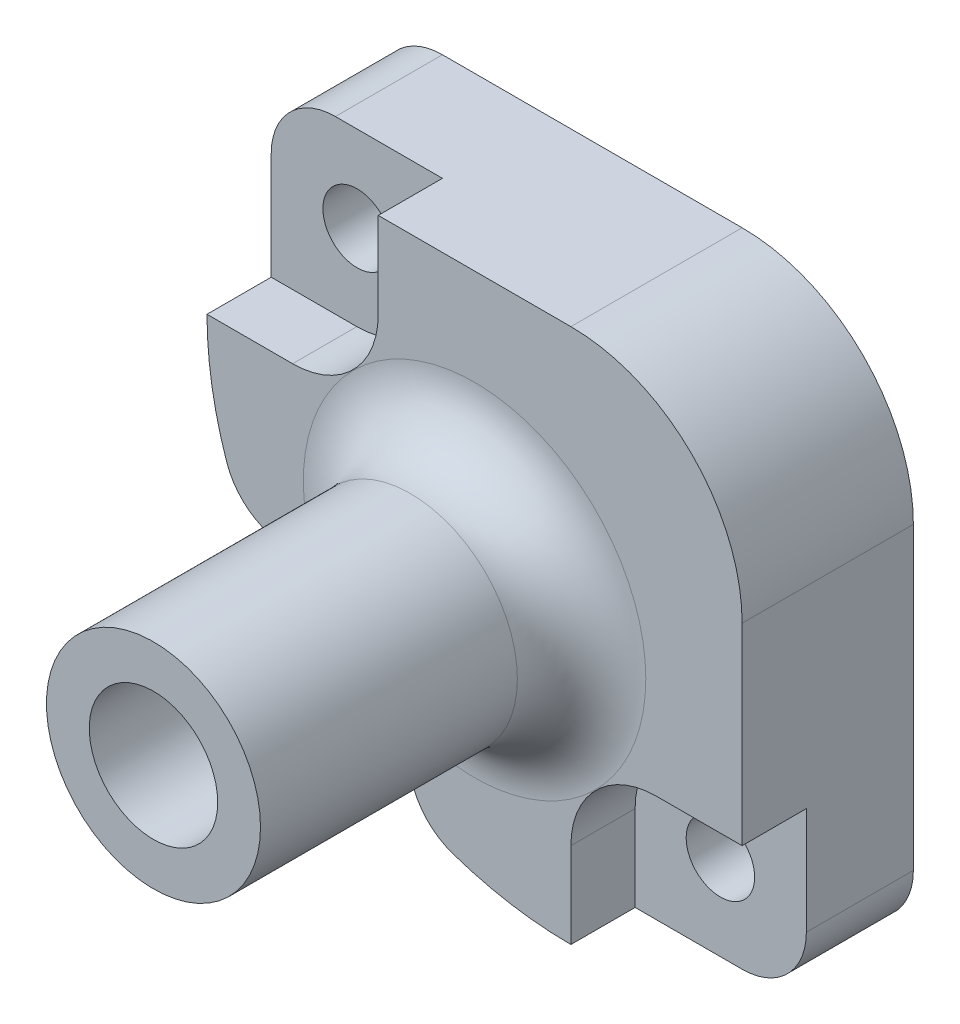
SolidWorks part; units mm, degrees
ref_plane "Piano frontale" through (0, 0, 0) normal (0, 0, 1) x (1, 0, 0)
ref_plane "Piano superiore" through (0, 0, 0) normal (0, 1, 0) x (1, 0, 0)
ref_plane "Piano destro" through (0, 0, 0) normal (1, 0, 0) x (0, 0, -1)
sketch "Schizzo1" plane through (0, 0, 0) normal (0, 0, 1) x (1, 0, 0)
  line L1 (-12.5, 12.5) -> (12.5, 12.5)
  line L2 (-12.5, 12.5) -> (-12.5, -12.5)
  line L3 (-12.5, -12.5) -> (12.5, -12.5)
  line L4 (12.5, 12.5) -> (12.5, -12.5)
  line L5 (-12.5, 12.5) -> (12.5, -12.5) construction
  line L6 (-12.5, -12.5) -> (12.5, 12.5) construction
  point P0 (0, 0)
  dimension "D1" = 25
extrude "Estrusione-Estrusione1" add sketch "Schizzo1" along normal blind 8
sketch "Schizzo8" plane through (0, 0, 8) normal (0, 0, 1) x (1, 0, 0)
  circle A0 centre (0, 0) radius 5
  dimension "D1" = 10
extrude "Estrusione-Estrusione3" add sketch "Schizzo8" along normal blind 15
fillet "Raccordo1" radius 3 1 edges at (5, 0, 8)
sketch "Schizzo9" plane through (0, 0, 0) normal (0, 0, -1) x (-1, 0, 0)
  circle A0 centre (0, 0) radius 1.6
  dimension "D1" = 3.2
extrude "Taglio-Estrusione2" cut sketch "Schizzo9" against normal up to next
sketch "Schizzo10" plane through (0, 0, 0) normal (0, 0, -1) x (-1, 0, 0)
  circle A0 centre (0, 0) radius 3
  dimension "D1" = 6
extrude "Taglio-Estrusione3" cut sketch "Schizzo10" against normal blind 4
sketch "Schizzo11" plane through (0, 0, 23) normal (0, 0, 1) x (1, 0, 0)
  circle A0 centre (0, 0) radius 3
  dimension "D1" = 6
extrude "Taglio-Estrusione4" cut sketch "Schizzo11" against normal blind 16
sketch "Schizzo13" plane through (0, 0, 0) normal (0, 0, -1) x (-1, 0, 0)
  line L0 (-12.5, -12.5) -> (12.5, 12.5) construction
  circle A0 centre (0, 0) radius 12 construction
  circle A1 centre (-8.4853, -8.4853) radius 1.6
  circle A2 centre (8.4853, 8.4853) radius 1.6
  dimension "D1" = 24
  dimension "D2" = 3.2
extrude "Taglio-Estrusione6" cut sketch "Schizzo13" against normal up to next
sketch "Schizzo17" plane through (0, 0, 8) normal (0, 0, 1) x (1, 0, 0)
  line L0 (-12.5, -12.5) -> (12.5, -12.5) construction
  line L1 (4.5, -12.5) -> (4.5, -8.5)
  line L2 (12.5, -4.5) -> (8.5, -4.5)
  line L3 (12.5, -12.5) -> (12.5, 12.5) construction
  line L4 (12.5, -12.5) -> (12.5, -4.5)
  line L5 (4.5, -12.5) -> (12.5, -12.5)
  arc A0 (4.5, -8.5) -> (8.5, -4.5) centre (8.5, -8.5) cw
  dimension "D1" = 4
  dimension "D2" = 8
extrude "Taglio-Estrusione8" cut sketch "Schizzo17" against normal blind 3 and the other way through all
pattern_circular "RipetizioneCircolare1" count 2 over 180 about axis through (0, 0, 0) along (0, 0, 1) of "Taglio-Estrusione8"
sketch "Schizzo20" plane through (0, 0, 8) normal (0, 0, 1) x (1, 0, 0)
  line L0 (-12.5, -12.5) -> (4.5, -12.5) construction
  line L1 (-12.5, -12.5) -> (4.5, -12.5)
  line L2 (-12.5, 4.5) -> (-12.5, -12.5) construction
  line L3 (-12.5, 4.5) -> (-12.5, -12.5)
  arc A0 (-12.5, 4.5) -> (-10.9357, -2.6231) centre (4.5, 4.5) ccw
  arc A1 (-10.9357, -2.6231) -> (-2.6231, -10.9357) centre (-12.5, -12.5) cw
  arc A2 (-2.6231, -10.9357) -> (4.5, -12.5) centre (4.5, 4.5) ccw
  dimension "D1" = 10
extrude "Taglio-Estrusione9" cut sketch "Schizzo20" against normal up to next and the other way up to next
fillet "Raccordo2" radius 3 2 edges at (-2.6231, -10.9357, 4) (-10.9357, -2.6231, 4)
fillet "Raccordo3" radius 3 2 edges at (12.5, -12.5, 2.5) (-12.5, 12.5, 2.5)
fillet "Raccordo4" radius 8 1 edges at (12.5, 12.5, 4)
